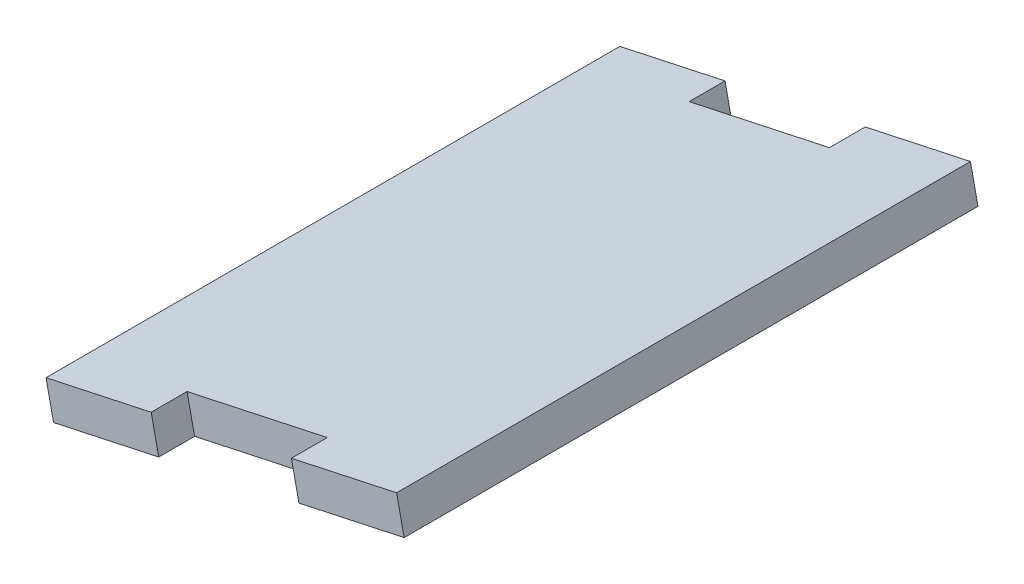
SolidWorks part; units mm, degrees
ref_plane "Front Plane" through (0, 0, 0) normal (0, 0, 1) x (1, 0, 0)
ref_plane "Top Plane" through (0, 0, 0) normal (0, 1, 0) x (1, 0, 0)
ref_plane "Right Plane" through (0, 0, 0) normal (1, 0, 0) x (0, 0, -1)
sketch "Sketch1" plane through (0, 0, 0) normal (0, 0, 1) x (1, 0, 0)
  line L0 (39.564, 294.4917) -> (40.2335, 291.3881)
  line L1 (40.2335, 291.3881) -> (71.2695, 298.0833)
  line L2 (71.2695, 298.0833) -> (70.6, 301.1869)
  line L3 (70.6, 301.1869) -> (39.564, 294.4917)
  point P2 (0, 0)
  dimension "D1" = 3.175
  dimension "D2" = 31.75
extrude "Boss-Extrude1" add sketch "Sketch1" against normal up to vertex (50.8 mm away) contours L1 L2 L3 L0
sketch "Sketch2" plane through (-58.9447, 273.241, 0) normal (-0.2109, 0.9775, 0) x (0.9775, 0.2109, 0)
  line L0 (132.5247, 50.8) -> (100.7747, 50.8) construction
  line L1 (110.2997, 50.8) -> (122.9997, 50.8)
  line L2 (110.2997, 50.8) -> (110.2997, 47.625)
  line L3 (110.2997, 47.625) -> (122.9997, 47.625)
  line L4 (122.9997, 50.8) -> (122.9997, 47.625)
  line L5 (59.6177, 47.625) -> (150.3585, 47.625) construction
  line L6 (132.5247, 0) -> (100.7747, 0) construction
  line L7 (110.2997, 0) -> (122.9997, 0)
  line L8 (110.2997, 0) -> (110.2997, 3.175)
  line L9 (110.2997, 3.175) -> (122.9997, 3.175)
  line L10 (122.9997, 0) -> (122.9997, 3.175)
  line L11 (150.3585, 3.175) -> (59.6177, 3.175) construction
  line L12 (100.7747, 50.8) -> (100.7747, 0) construction
  line L13 (132.5247, 50.8) -> (132.5247, 0) construction
  dimension "D1" = 9.525
  dimension "D2" = 9.525
  dimension "D3" = 9.525
  dimension "D4" = 9.525
extrude "Cut-Extrude1" cut sketch "Sketch2" against normal blind 3.175
